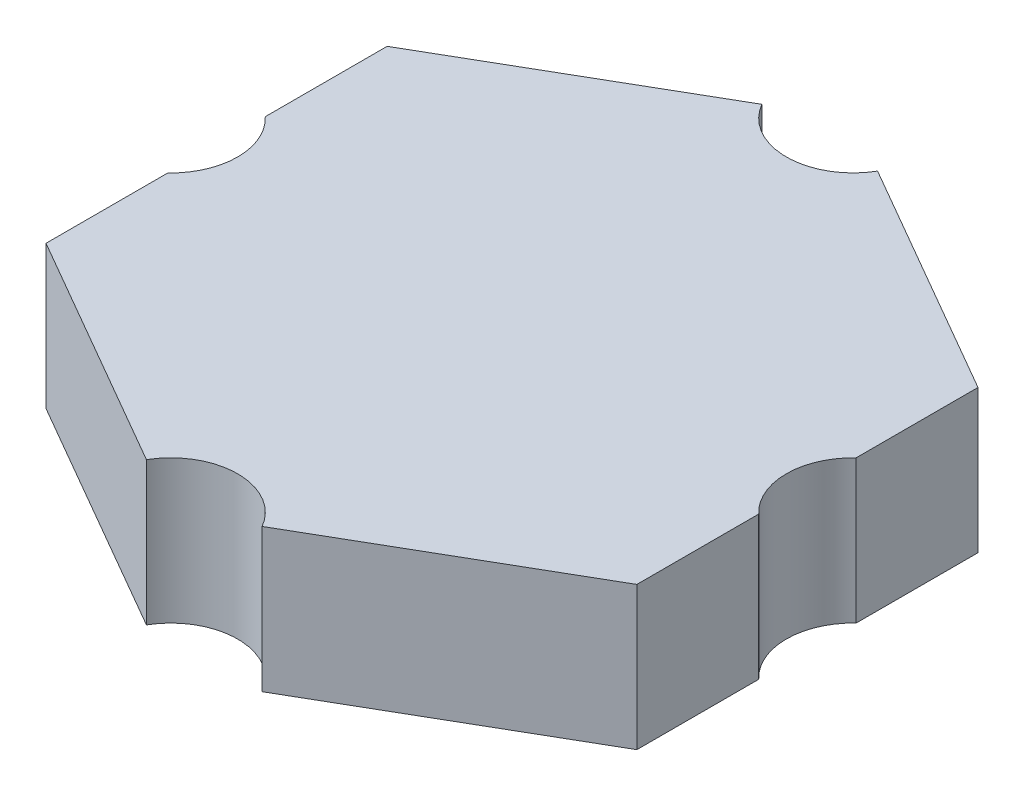
SolidWorks part; units mm, degrees
ref_plane "Front Plane" through (0, 0, 0) normal (0, 0, 1) x (1, 0, 0)
ref_plane "Top Plane" through (0, 0, 0) normal (0, 1, 0) x (1, 0, 0)
ref_plane "Right Plane" through (0, 0, 0) normal (1, 0, 0) x (0, 0, -1)
sketch "Sketch2" plane through (0, 0, 0) normal (0, 1, 0) x (1, 0, 0)
  line L1 (0, 7.15) -> (-6.1921, 3.575)
  line L2 (-6.1921, 3.575) -> (-6.1921, -3.575)
  line L3 (-6.1921, -3.575) -> (0, -7.15)
  line L4 (0, -7.15) -> (6.1921, -3.575)
  line L5 (6.1921, -3.575) -> (6.1921, 3.575)
  line L6 (6.1921, 3.575) -> (0, 7.15)
  circle A0 centre (0, 0) radius 6.1921 construction
  dimension "D1" = 7.15
extrude "Boss-Extrude1" add sketch "Sketch2" along normal blind 3
sketch "Sketch3" plane through (0, 3, 0) normal (0, 1, 0) x (1, 0, 0)
  circle A0 centre (0, 7.15) radius 1.4
  circle A1 centre (7.15, 0) radius 1.4
  circle A2 centre (0, -7.15) radius 1.4
  circle A3 centre (-7.15, 0) radius 1.4
  dimension "D1" = 2.8
  dimension "D2" = 4
extrude "Cut-Extrude1" cut sketch "Sketch3" against normal blind 9.45
